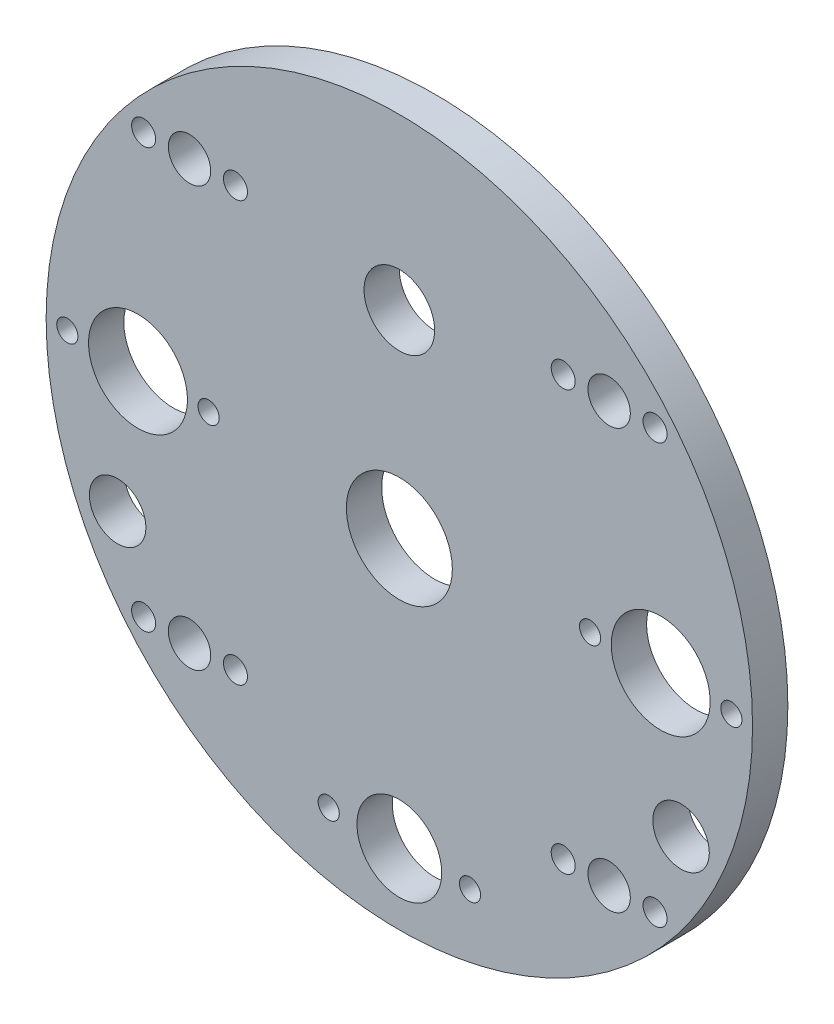
SolidWorks part; units mm, degrees
material "Acrylic (Medium-high impact)"
ref_plane "Front Plane" through (0, 0, 0) normal (0, 0, 1) x (1, 0, 0)
ref_plane "Top Plane" through (0, 0, 0) normal (0, 1, 0) x (1, 0, 0)
ref_plane "Right Plane" through (0, 0, 0) normal (1, 0, 0) x (0, 0, -1)
sketch "Sketch1" plane through (0, 0, 0) normal (0, 0, 1) x (1, 0, 0)
  circle A0 centre (0, 0) radius 50
  dimension "D1" = 100
extrude "Boss-Extrude1" add sketch "Sketch1" along normal blind 5
hole_wizard "Ø14.0 (14) Diameter Hole1" positions "Sketch5" profile "Sketch6" hole size "Ø14.0" standard "ISO"
sketch "Sketch5" plane through (0, 0, 0) normal (0, 0, -1) x (-1, 0, 0)
  point P4 (37, 0)
  point P17 (-37, 0)
  point P21 (0, -37) [skipped]
  dimension "D1" = 3
  dimension "D3" = 37
sketch "Sketch6" plane through (-37, 0, 0) normal (1, 0, 0) x (0, 1, 0)
  line L0 (0, 0) -> (0, 5)
  line L1 (0, 5) -> (7, 5)
  line L2 (7, 5) -> (7, 0)
  line L5 (7, 0) -> (0, 0)
  line L11 (0, -6.35) -> (0, 107.95) construction
  dimension "Thru Hole Dia." = 14
  dimension "Thru Hole Depth" = 5
sketch "Sketch7" plane through (0, 0, 5) normal (0, 0, 1) x (1, 0, 0)
  circle A0 centre (0, 26) radius 5
  dimension "D1" = 10
  dimension "D2" = 26
extrude "Cut-Extrude1" cut sketch "Sketch7" against normal blind 10
sketch "Sketch8" plane through (0, 0, 5) normal (0, 0, 1) x (1, 0, 0)
  line L0 (0, 0) -> (-37, 0) construction
  line L1 (0, 0) -> (-29.6985, 29.6985) construction
  circle A0 centre (-29.6985, 29.6985) radius 3
  dimension "D3" = 6
  dimension "D1" = 42
  dimension "D2" = 45
extrude "Cut-Extrude2" cut sketch "Sketch8" against normal blind 10
pattern_circular "CirPattern1" count 4 over 360 about axis through (0, 0, 0) along (0, 0, 1) of "Cut-Extrude2"
sketch "Sketch9" plane through (0, 0, 5) normal (0, 0, 1) x (1, 0, 0)
  circle A0 centre (0, -2) radius 7.5
  dimension "D1" = 15
  dimension "D2" = 2
extrude "Cut-Extrude3" cut sketch "Sketch9" against normal blind 10
sketch "Sketch10" plane through (0, 0, 5) normal (0, 0, 1) x (1, 0, 0)
  circle A0 centre (-47, 0) radius 1.5
  circle A1 centre (-27, 0) radius 1.5
  circle A2 centre (27, 0) radius 1.5
  circle A3 centre (47, 0) radius 1.5
  circle A4 centre (10, -40) radius 1.5
  circle A5 centre (-10, -40) radius 1.5
  circle A6 centre (-37, 0) radius 7 construction
  circle A7 centre (37, 0) radius 7 construction
  circle A9 centre (0, -40) radius 6
  dimension "D1" = 3
  dimension "D2" = 3
  dimension "D3" = 3
  dimension "D4" = 3
  dimension "D5" = 3
  dimension "D6" = 3
  dimension "D8" = 10
  dimension "D9" = 10
  dimension "D10" = 10
  dimension "D11" = 10
  dimension "D12" = 10
  dimension "D15" = 12
  dimension "D16" = 40
  dimension "D7" = 10
  dimension "D13" = 40
  dimension "D14" = 40
extrude "Cut-Extrude4" cut sketch "Sketch10" against normal blind 10
sketch "Sketch12" plane through (0, 0, 5) normal (0, 0, 1) x (1, 0, 0)
  line L0 (0, 0) -> (-39.8775, -18.5952) construction
  line L1 (0, 0) -> (-59.2279, 0) construction
  circle A0 centre (-39.8775, -18.5952) radius 4
  dimension "D1" = 8
  dimension "D2" = 44
  dimension "D3" = 25
extrude "Cut-Extrude5" cut sketch "Sketch12" against normal blind 10
mirror "Mirror1" about plane through (0, 0, 0) normal (1, 0, 0) of "Cut-Extrude5"
hole_wizard "M3 Clearance Hole1" positions "Sketch13" profile "Sketch14" hole size "M3" standard "ISO" end condition through all
sketch "Sketch13" plane through (0, 0, 5) normal (0, 0, 1) x (1, 0, 0)
  circle A1 centre (-29.6985, -29.6985) radius 3 construction
  point P0 (-36.1985, -29.6985)
  point P2 (-23.1985, -29.6985)
  dimension "D1" = 6
  dimension "D2" = 13
  dimension "D3" = 6.5
sketch "Sketch14" plane through (-36.1985, -29.6985, 5) normal (1, 0, 0) x (0, -1, 0)
  line L0 (0, 0) -> (0, 5)
  line L1 (0, 5) -> (1.7, 5)
  line L2 (1.7, 5) -> (1.7, 0)
  line L5 (1.7, 0) -> (0, 0)
  line L11 (0, -6.35) -> (0, 107.95) construction
  dimension "Thru Hole Dia." = 3.4
  dimension "Thru Hole Depth" = 5
mirror "Mirror2" about plane through (0, 0, 0) normal (0, 1, 0) of "M3 Clearance Hole1"
mirror "Mirror3" about plane through (0, 0, 0) normal (1, 0, 0) of "Mirror2", "M3 Clearance Hole1"
